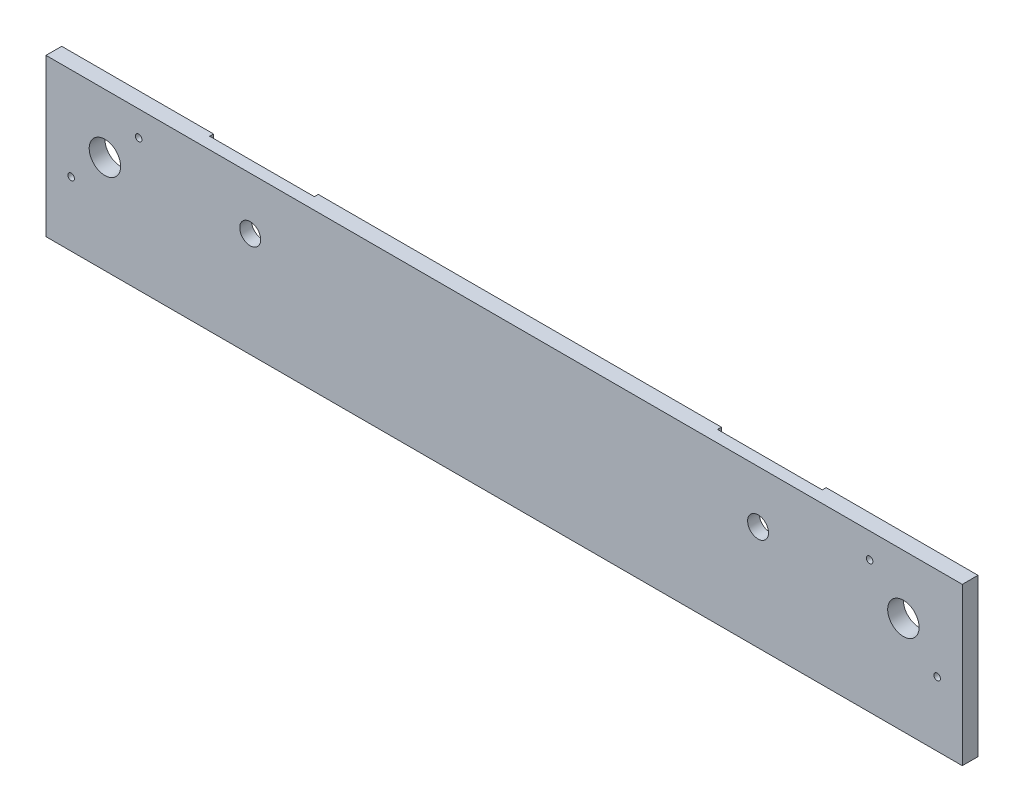
SolidWorks part; units mm, degrees
ref_plane "Alzado" through (0, 0, 0) normal (0, 0, 1) x (1, 0, 0)
ref_plane "Planta" through (0, 0, 0) normal (0, 1, 0) x (1, 0, 0)
ref_plane "Vista lateral" through (0, 0, 0) normal (1, 0, 0) x (0, 0, -1)
sketch "Croquis1" plane through (0, 0, 0) normal (0, 0, 1) x (1, 0, 0)
  line L1 (-350, -60) -> (0, -60)
  line L2 (-350, -60) -> (-350, 0)
  line L3 (-350, 0) -> (0, 0)
  line L4 (0, -60) -> (0, 0)
  dimension "D1" = 350
  dimension "D2" = 60
extrude "Saliente-Extruir1" add sketch "Croquis1" along normal blind 6 contours L3 L4 L1 L2
sketch "Croquis2" plane through (0, 0, 6) normal (0, 0, 1) x (1, 0, 0)
  line L0 (-350, -60) -> (-350, 0) construction
  line L1 (0, -60) -> (0, 0) construction
  line L2 (-350, -60) -> (0, -60) construction
  line L3 (-340.4047, -35.4047) -> (-314.5953, -9.5953) construction
  line L4 (-35.4047, -9.5953) -> (-9.5953, -35.4047) construction
  line L5 (-350, 0) -> (0, 0) construction
  circle A0 centre (-327.5, -22.5) radius 6
  circle A1 centre (-22.5, -22.5) radius 6
  circle A2 centre (-327.5, -22.5) radius 18.25 construction
  circle A4 centre (-314.5953, -9.5953) radius 1.25
  circle A5 centre (-340.4047, -35.4047) radius 1.25
  circle A6 centre (-22.5, -22.5) radius 18.25 construction
  circle A7 centre (-35.4047, -9.5953) radius 1.25
  circle A8 centre (-9.5953, -35.4047) radius 1.25
  dimension "D1" = 12
  dimension "D2" = 12
  dimension "D7" = 36.5
  dimension "D9" = 2.5
  dimension "D10" = 2.5
  dimension "D11" = 36.5
  dimension "D13" = 2.5
  dimension "D14" = 2.5
  dimension "D3" = 22.5
  dimension "D4" = 22.5
  dimension "D5" = 22.5
  dimension "D6" = 22.5
  dimension "D8" = 45
  dimension "D12" = 45
extrude "Cortar-Extruir1" cut sketch "Croquis2" against normal through all
sketch "Croquis3" plane through (0, 0, 0) normal (0, 0, 1) x (1, 0, 0)
  line L0 (-350, 0) -> (0, 0) construction
  line L1 (-98, 0) -> (-58, 0)
  line L2 (-98, 0) -> (-98, -36)
  line L3 (-94, -40) -> (-62, -40)
  line L4 (-58, 0) -> (-58, -36)
  line L5 (0, -60) -> (0, 0) construction
  line L6 (-292, 0) -> (-252, 0)
  line L7 (-292, 0) -> (-292, -36)
  line L8 (-288, -40) -> (-256, -40)
  line L9 (-252, 0) -> (-252, -36)
  line L10 (-350, -60) -> (-350, 0) construction
  arc A0 (-98, -36) -> (-94, -40) centre (-94, -36) ccw
  arc A1 (-62, -40) -> (-58, -36) centre (-62, -36) ccw
  arc A2 (-292, -36) -> (-288, -40) centre (-288, -36) ccw
  arc A3 (-256, -40) -> (-252, -36) centre (-256, -36) ccw
  dimension "D4" = 8
  dimension "D5" = 8
  dimension "D8" = 8
  dimension "D9" = 8
  dimension "D1" = 58
  dimension "D2" = 40
  dimension "D3" = 40
  dimension "D6" = 40
  dimension "D7" = 40
  dimension "D10" = 58
extrude "Cortar-Extruir4" cut sketch "Croquis3" along normal blind 1.5 from surface at 0 starting at face at (-8.3453, -35.4047, 0)
sketch "Croquis4" plane through (0, 0, 6) normal (0, 0, 1) x (1, 0, 0)
  line L0 (-350, -60) -> (-350, 0) construction
  line L1 (0, -60) -> (0, 0) construction
  line L2 (-350, 0) -> (0, 0) construction
  circle A0 centre (-272, -20) radius 4
  circle A1 centre (-78, -20) radius 4
  dimension "D1" = 8
  dimension "D2" = 8
  dimension "D3" = 78
  dimension "D4" = 78
  dimension "D5" = 20
  dimension "D6" = 20
extrude "Cortar-Extruir5" cut sketch "Croquis4" against normal through all
